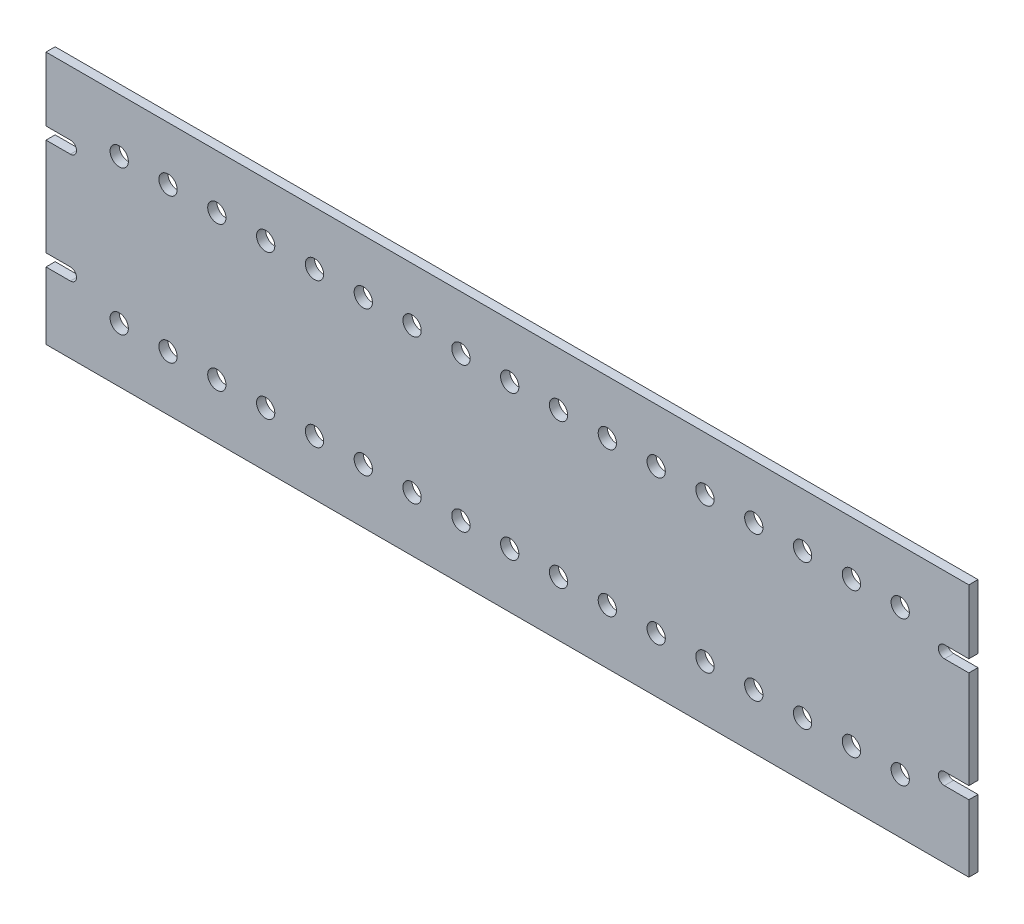
SolidWorks part; units mm, degrees
ref_plane "Front Plane" through (0, 0, 0) normal (0, 0, 1) x (1, 0, 0)
ref_plane "Top Plane" through (0, 0, 0) normal (0, 1, 0) x (1, 0, 0)
ref_plane "Right Plane" through (0, 0, 0) normal (1, 0, 0) x (0, 0, -1)
sketch "Sketch1" plane through (0, 0, 0) normal (0, 0, 1) x (1, 0, 0)
  line L0 (0, 98.425) -> (12.7, 98.425)
  line L1 (0, 0) -> (480.2188, 0)
  line L2 (0, 0) -> (0, 131.7625) construction
  line L3 (0, 131.7625) -> (480.2188, 131.7625)
  line L4 (480.2188, 0) -> (480.2188, 131.7625) construction
  line L5 (12.7, 92.075) -> (0, 92.075)
  line L6 (12.7, 98.425) -> (12.7, 92.075) construction
  line L7 (0, 41.275) -> (12.7, 41.275)
  line L8 (12.7, 34.925) -> (0, 34.925)
  line L9 (12.7, 41.275) -> (12.7, 34.925) construction
  line L10 (480.2188, 98.425) -> (467.5187, 98.425)
  line L11 (467.5187, 92.075) -> (480.2188, 92.075)
  line L12 (467.5187, 98.425) -> (467.5187, 92.075) construction
  line L13 (480.2188, 41.275) -> (467.5187, 41.275)
  line L14 (467.5187, 34.925) -> (480.2188, 34.925)
  line L15 (467.5187, 41.275) -> (467.5187, 34.925) construction
  line L16 (480.2188, 131.7625) -> (480.2188, 98.425)
  line L17 (480.2188, 92.075) -> (480.2188, 41.275)
  line L18 (480.2188, 34.925) -> (480.2188, 0)
  line L19 (0, 34.925) -> (0, 0)
  line L20 (0, 41.275) -> (0, 92.075)
  line L21 (0, 98.425) -> (0, 131.7625)
  line L22 (0, 103.8245) -> (480.2188, 103.8245) construction
  line L23 (0, 28.5757) -> (480.2188, 28.5757) construction
  line L24 (38.1, 103.8245) -> (38.1, 28.5757) construction
  arc A0 (12.7, 98.425) -> (12.7, 92.075) centre (12.7, 95.25) cw
  arc A1 (12.7, 41.275) -> (12.7, 34.925) centre (12.7, 38.1) cw
  arc A2 (467.5187, 98.425) -> (467.5187, 92.075) centre (467.5187, 95.25) ccw
  arc A3 (467.5187, 41.275) -> (467.5187, 34.925) centre (467.5187, 38.1) ccw
  circle A4 centre (38.1, 103.8245) radius 4.7625
  circle A5 centre (38.1, 28.5757) radius 4.7625
  circle A6 centre (63.5, 103.8245) radius 4.7625
  circle A7 centre (63.5, 28.5757) radius 4.7625
  circle A8 centre (88.9, 103.8245) radius 4.7625
  circle A9 centre (88.9, 28.5757) radius 4.7625
  circle A10 centre (114.3, 103.8245) radius 4.7625
  circle A11 centre (114.3, 28.5757) radius 4.7625
  circle A12 centre (139.7, 103.8245) radius 4.7625
  circle A13 centre (139.7, 28.5757) radius 4.7625
  circle A14 centre (165.1, 103.8245) radius 4.7625
  circle A15 centre (165.1, 28.5757) radius 4.7625
  circle A16 centre (190.5, 103.8245) radius 4.7625
  circle A17 centre (190.5, 28.5757) radius 4.7625
  circle A18 centre (215.9, 103.8245) radius 4.7625
  circle A19 centre (215.9, 28.5757) radius 4.7625
  circle A20 centre (241.3, 103.8245) radius 4.7625
  circle A21 centre (241.3, 28.5757) radius 4.7625
  circle A22 centre (266.7, 103.8245) radius 4.7625
  circle A23 centre (266.7, 28.5757) radius 4.7625
  circle A24 centre (292.1, 103.8245) radius 4.7625
  circle A25 centre (292.1, 28.5757) radius 4.7625
  circle A26 centre (317.5, 103.8245) radius 4.7625
  circle A27 centre (317.5, 28.5757) radius 4.7625
  circle A28 centre (342.9, 103.8245) radius 4.7625
  circle A29 centre (342.9, 28.5757) radius 4.7625
  circle A30 centre (368.3, 103.8245) radius 4.7625
  circle A31 centre (368.3, 28.5757) radius 4.7625
  circle A32 centre (393.7, 103.8245) radius 4.7625
  circle A33 centre (393.7, 28.5757) radius 4.7625
  circle A34 centre (419.1, 103.8245) radius 4.7625
  circle A35 centre (419.1, 28.5757) radius 4.7625
  circle A36 centre (444.5, 103.8245) radius 4.7625
  circle A37 centre (444.5, 28.5757) radius 4.7625
  dimension "D1" = 17
extrude "Boss-Extrude1" add sketch "Sketch1" along normal blind 4.7625
ref_plane "Plane1" through (240.1094, 0, 0) normal (-1, 0, 0) x (0, 0, 1)
